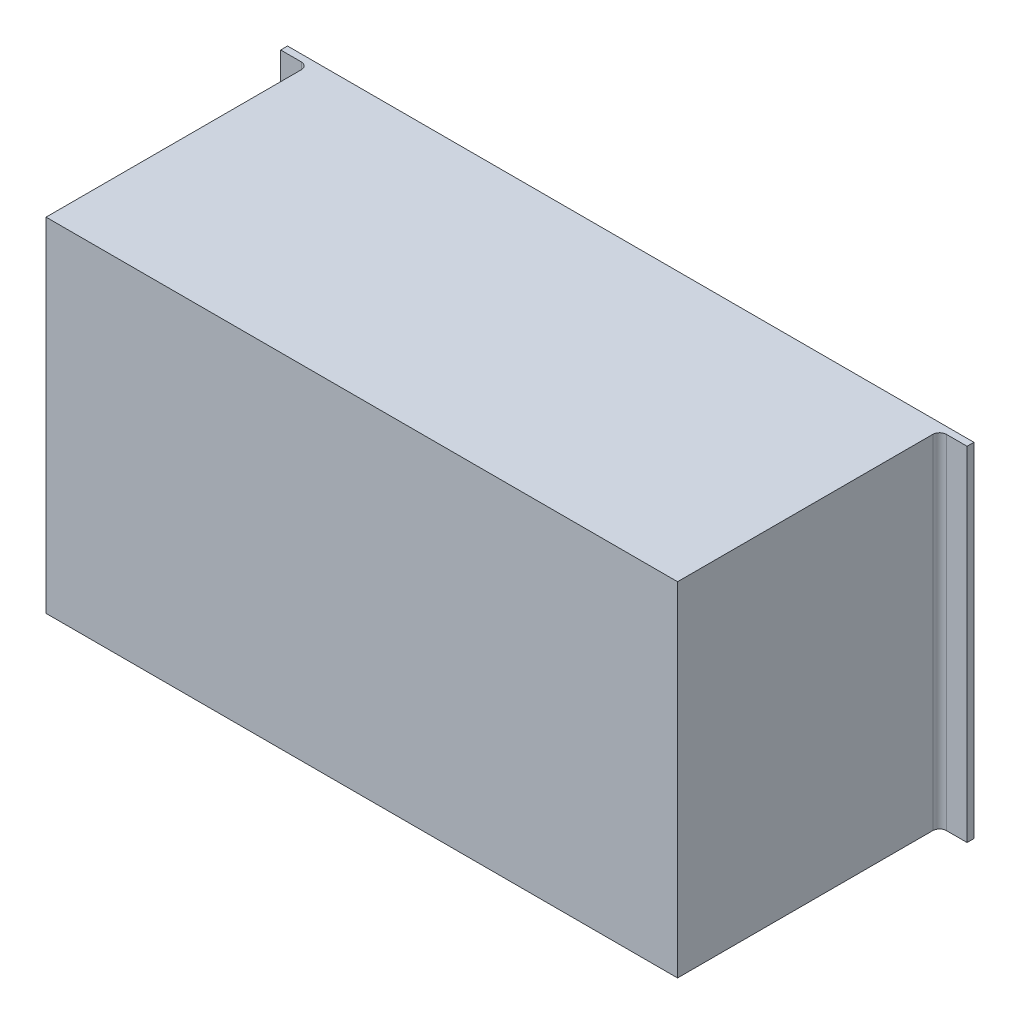
SolidWorks part; units mm, degrees
material "6061 Alaşım"
ref_plane "Ön Düzlem" through (0, 0, 0) normal (0, 0, 1) x (1, 0, 0)
ref_plane "Üst Düzlem" through (0, 0, 0) normal (0, 1, 0) x (1, 0, 0)
ref_plane "Sağ Düzlem" through (0, 0, 0) normal (1, 0, 0) x (0, 0, -1)
other "Kütle Merkezi"
sketch "Çizim1" plane through (0, 0, 0) normal (0, 0, 1) x (1, 0, 0)
  line L1 (0, 0) -> (920, 0)
  line L2 (0, 0) -> (0, 500)
  line L3 (0, 500) -> (920, 500)
  line L4 (920, 0) -> (920, 500)
  dimension "D1" = 500
  dimension "D2" = 920
extrude "Yükseklik-Ekstrüzyon1" add sketch "Çizim1" along normal blind 380 contours L2 L1 L4 L3
shell "İç Boşaltma1" thickness 0.6
sketch "Çizim2" plane through (0, 0, 380) normal (0, 0, 1) x (1, 0, 0)
  line L1 (0, 0) -> (920, 0)
  line L2 (0, 0) -> (0, 500)
  line L3 (0, 500) -> (920, 500)
  line L4 (920, 0) -> (920, 500)
extrude "Yükseklik-Ekstrüzyon2" add sketch "Çizim2" along normal blind 1.8
sketch "Çizim3" plane through (0, 0, 0) normal (0, 0, -1) x (-1, 0, 0)
  line L0 (0, 500) -> (-920, 500) construction
  line L1 (-960, 0) -> (40, 0)
  line L2 (-960, 0) -> (-960, 500)
  line L3 (-960, 500) -> (40, 500)
  line L4 (40, 0) -> (40, 500)
  line L5 (-920, 0) -> (-920, 500) construction
  dimension "D1" = 1000
  dimension "D2" = 40
extrude "Yükseklik-Ekstrüzyon3" add sketch "Çizim3" along normal blind 10
fillet "Radyus1" radius 10 2 edges at (0, 250, 0) (920, 250, 0)
sketch "Çizim4" plane through (0, 0, 0.6) normal (0, 0, 1) x (1, 0, 0)
  line L8 (919.4, 499.4) -> (0.6, 499.4)
  line L9 (0.6, 499.4) -> (0.6, 0.6)
  line L10 (0.6, 0.6) -> (919.4, 0.6)
  line L11 (919.4, 0.6) -> (919.4, 499.4)
  line L12 (919.4, 499.4) -> (0.6, 499.4)
  line L13 (0.6, 499.4) -> (0.6, 0.6)
  line L14 (0.6, 0.6) -> (919.4, 0.6)
  line L15 (919.4, 0.6) -> (919.4, 499.4)
  dimension "D1" = 0
extrude "Kes-Ekstrüzyon1" cut sketch "Çizim4" against normal blind 5
fillet "Radyus2" radius 20 4 edges at (460, 0.6, -4.4) (0.6, 250, -4.4) (460, 499.4, -4.4) (919.4, 250, -4.4)
sketch "Çizim5" plane through (0, 0, -10) normal (0, 0, -1) x (-1, 0, 0)
  line L0 (-960, 0) -> (40, 0) construction
  line L1 (-920, 0) -> (0, 0)
  line L2 (-920, 0) -> (-920, 500)
  line L3 (-920, 500) -> (0, 500)
  line L4 (0, 0) -> (0, 500)
  line L5 (40, 500) -> (-960, 500) construction
  line L6 (-960, 500) -> (-960, 0) construction
  line L7 (40, 0) -> (40, 500) construction
  dimension "D1" = 40
  dimension "D2" = 40
extrude "Kes-Ekstrüzyon2" cut sketch "Çizim5" against normal blind 0.0001 contours L2 L1 L4 L3
